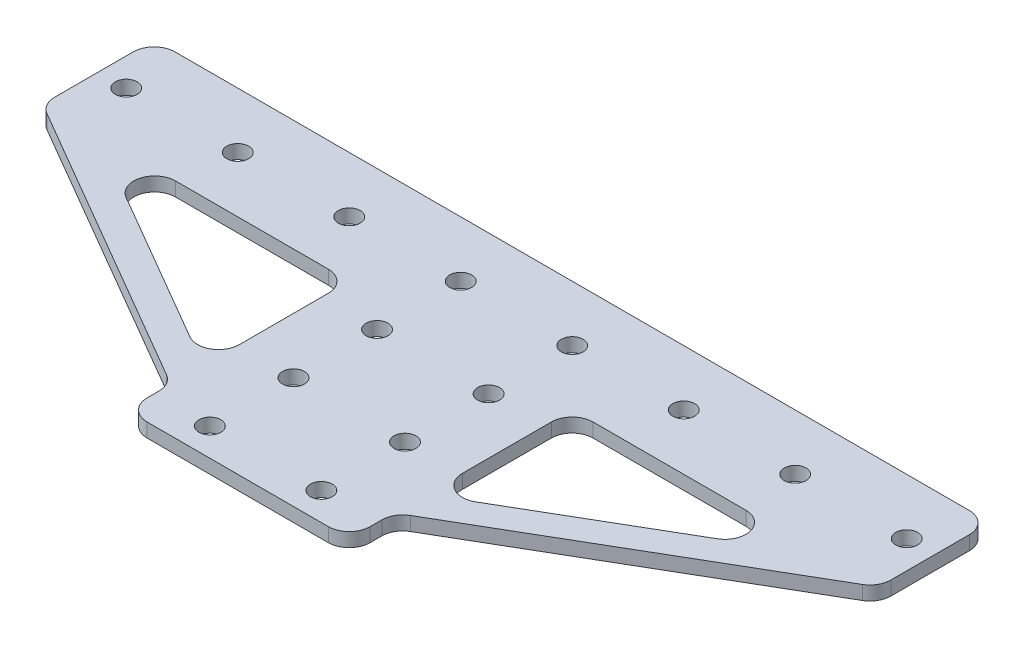
SolidWorks part; units mm, degrees
material "6061-T6 (SS)"
ref_plane "Front Plane" through (0, 0, 0) normal (0, 0, 1) x (1, 0, 0)
ref_plane "Top Plane" through (0, 0, 0) normal (0, 1, 0) x (1, 0, 0)
ref_plane "Right Plane" through (0, 0, 0) normal (1, 0, 0) x (0, 0, -1)
sketch "Sketch1" plane through (0, 0, 0) normal (0, 1, 0) x (1, 0, 0)
  line L0 (95.25, 0) -> (95.25, -50.8) construction
  line L1 (0, 0) -> (190.5, 0)
  line L2 (0, 0) -> (0, 25.4)
  line L3 (0, 25.4) -> (190.5, 25.4)
  line L4 (190.5, 0) -> (190.5, 25.4)
  line L5 (69.85, 0) -> (120.65, 0)
  line L6 (69.85, 0) -> (69.85, -50.8)
  line L7 (69.85, -50.8) -> (120.65, -50.8)
  line L8 (120.65, 0) -> (120.65, -50.8)
  line L9 (0, 0) -> (69.85, -40.64)
  line L10 (12.6269, 0) -> (69.85, -33.2934)
  line L11 (177.8731, 0) -> (120.65, -33.2934)
  line L12 (190.5, 0) -> (120.65, -40.64)
  line L13 (0, 12.7) -> (190.5, 12.7) construction
  circle A0 centre (6.35, 12.7) radius 2.4892
  circle A1 centre (31.75, 12.7) radius 2.4892
  circle A2 centre (57.15, 12.7) radius 2.4892
  circle A3 centre (82.55, 12.7) radius 2.4892
  circle A4 centre (107.95, 12.7) radius 2.4892
  circle A5 centre (133.35, 12.7) radius 2.4892
  circle A6 centre (158.75, 12.7) radius 2.4892
  circle A7 centre (184.15, 12.7) radius 2.4892
  circle A23 centre (82.55, -6.35) radius 2.4892
  circle A25 centre (107.95, -6.35) radius 2.4892
  circle A27 centre (107.95, -25.4) radius 2.4892
  circle A35 centre (107.95, -44.45) radius 2.4892
  circle A36 centre (82.55, -25.4) radius 2.4892
  circle A37 centre (82.55, -44.45) radius 2.4892
  point P21 (108.5075, -6.35)
  point P24 (0, 0)
  point P26 (0, 0)
  point P50 (0, 0)
  point P51 (0, 0)
  point P52 (0, 0)
  point P53 (0, 0)
  point P54 (0, 0)
  point P55 (0, 0)
  point P56 (0, 0)
  dimension "D8" = 4.9784
  dimension "D1" = 50.8
  dimension "D2" = 190.5
  dimension "D3" = 25.4
  dimension "D4" = 6.35
  dimension "D5" = 10.16
  dimension "D6" = 2
  dimension "D7" = 3
  dimension "D10" = 25.4
  dimension "D11" = 6.35
  dimension "D12" = 19.05
  dimension "D13" = 19.05
  dimension "D9" = 8
extrude "Boss-Extrude1" add sketch "Sketch1" along normal blind 3.175
fillet "Fillet1" radius 4.7625 14 edges at (120.65, 1.5875, 0) (120.65, 1.5875, 33.2934) (177.8731, 1.5875, 0) (69.85, 1.5875, 33.2934) (69.85, 1.5875, 0) (12.6269, 1.5875, 0) (120.65, 1.5875, 40.64) (120.65, 1.5875, 50.8) (69.85, 1.5875, 50.8) (69.85, 1.5875, 40.64) (0, 1.5875, -25.4) (190.5, 1.5875, -25.4) (190.5, 1.5875, 0) (0, 1.5875, 0)
